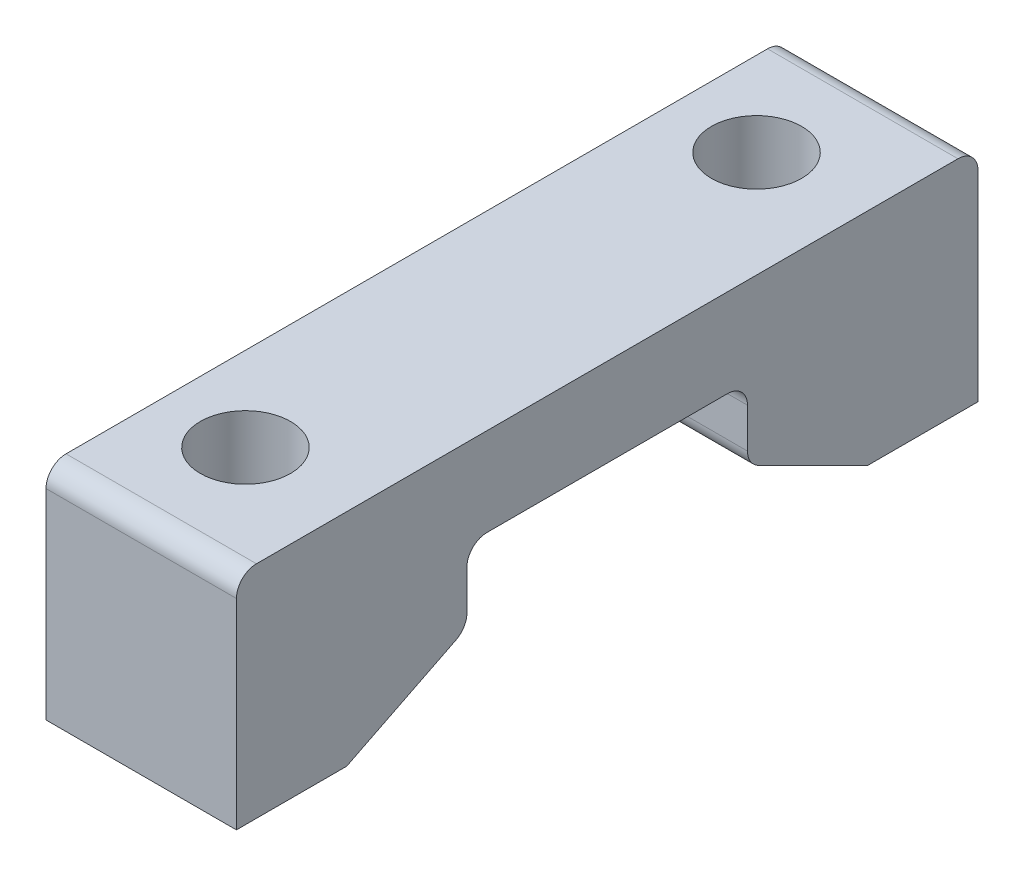
SolidWorks part; units mm, degrees
ref_plane "Front Plane" through (0, 0, 0) normal (0, 0, 1) x (1, 0, 0)
ref_plane "Top Plane" through (0, 0, 0) normal (0, 1, 0) x (1, 0, 0)
ref_plane "Right Plane" through (0, 0, 0) normal (1, 0, 0) x (0, 0, -1)
sketch "Sketch1" plane through (0, 0, 0) normal (1, 0, 0) x (0, 0, -1)
  line L0 (-7, 1.1) -> (7, 1.1)
  line L1 (18.5, -5.5) -> (-18.5, -5.5) construction
  line L2 (18.5, -5.5) -> (18.5, 5.5)
  line L3 (18.5, 5.5) -> (-18.5, 5.5)
  line L4 (-18.5, -5.5) -> (-18.5, 5.5)
  line L5 (18.5, -5.5) -> (-18.5, 5.5) construction
  line L6 (18.5, 5.5) -> (-18.5, -5.5) construction
  line L7 (0, 1.1) -> (0, -5.5) construction
  line L8 (-7, 1.1) -> (-7, -2.5)
  line L9 (-7, -2.5) -> (-13, -5.5)
  line L10 (-13, -5.5) -> (-18.5, -5.5)
  line L11 (7, 1.1) -> (7, -2.5)
  line L12 (7, -2.5) -> (13, -5.5)
  line L13 (13, -5.5) -> (18.5, -5.5)
  line L14 (-7, -2.5) -> (7, -2.5) construction
  point P0 (0, 0)
  dimension "D1" = 37
  dimension "D2" = 11
  dimension "D3" = 14
  dimension "D4" = 6.6
  dimension "D5" = 3
  dimension "D6" = 6
extrude "Boss-Extrude1" add sketch "Sketch1" along normal blind 9.5
sketch "Sketch2" plane through (0, 5.5, 0) normal (0, 1, 0) x (1, 0, 0)
  line L0 (4.2, -12.75) -> (4.2, 12.75) construction
  line L1 (4.2, -12.75) -> (4.2, -18.5) construction
  line L2 (9.5, -18.5) -> (0, -18.5) construction
  line L3 (4.2, 12.75) -> (4.2, 18.5) construction
  line L4 (9.5, 18.5) -> (0, 18.5) construction
  line L5 (0, 18.5) -> (0, -18.5) construction
  circle A0 centre (4.2, -12.75) radius 2.25
  circle A1 centre (4.2, 12.75) radius 2.25
  dimension "D1" = 25.5
  dimension "D3" = 4.5
  dimension "D2" = 4.2
extrude "Cut-Extrude1" cut sketch "Sketch2" against normal through all
fillet "Fillet1" radius 1 6 edges at (4.75, 5.5, -18.5) (4.75, 5.5, 18.5) (4.75, -2.5, -7) (4.75, -2.5, 7) (4.75, 1.1, 7) (4.75, 1.1, -7)
